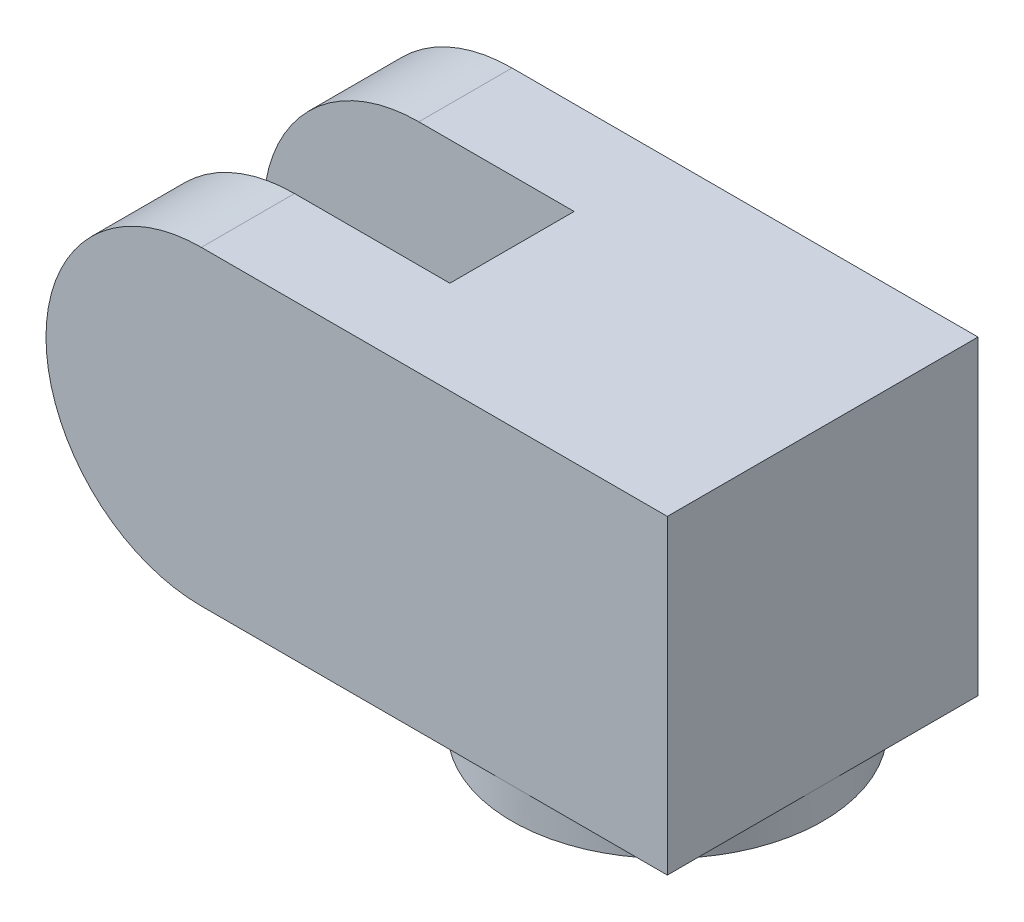
SolidWorks part; units mm, degrees
ref_plane "前视基准面" through (0, 0, 0) normal (0, 0, 1) x (1, 0, 0)
ref_plane "上视基准面" through (0, 0, 0) normal (0, 1, 0) x (1, 0, 0)
ref_plane "右视基准面" through (0, 0, 0) normal (1, 0, 0) x (0, 0, -1)
sketch "草图1" plane through (0, 0, 0) normal (0, 1, 0) x (1, 0, 0)
  line L1 (-5, 5) -> (5, 5)
  line L2 (-5, 5) -> (-5, -5)
  line L3 (-5, -5) -> (5, -5)
  line L4 (5, 5) -> (5, -5)
  dimension "D1" = 10
  dimension "D2" = 10
  dimension "D3" = 5
  dimension "D4" = 5
extrude "凸台-拉伸1" add sketch "草图1" along normal blind 10
sketch "草图2" plane through (-5, 0, 0) normal (-1, 0, 0) x (0, 0, 1)
  line L0 (-5, 0) -> (5, 0) construction
  line L1 (-5, 10) -> (-2, 10)
  line L2 (-5, 10) -> (-5, 0)
  line L3 (-5, 0) -> (-2, 0)
  line L4 (-2, 10) -> (-2, 0)
  line L6 (5, 0) -> (2, 0)
  line L7 (5, 0) -> (5, 10)
  line L8 (5, 10) -> (2, 10)
  line L9 (2, 0) -> (2, 10)
  dimension "D1" = 3
  dimension "D2" = 3
extrude "凸台-拉伸2" add sketch "草图2" along normal blind 10
sketch "草图3" plane through (0, 0, 5) normal (0, 0, 1) x (1, 0, 0)
  line L1 (-10, 10) -> (-17.0189, 10)
  line L3 (-10, 0) -> (-17.0189, 0)
  line L4 (-17.0189, 10) -> (-17.0189, 0)
  arc A0 (-10, 10) -> (-10, 0) centre (-10, 5) ccw
extrude "切除-拉伸1" cut sketch "草图3" against normal blind 10
sketch "草图4" plane through (0, 0, 0) normal (0, -1, 0) x (1, 0, 0)
  circle A0 centre (0, 0) radius 5
extrude "凸台-拉伸3" add sketch "草图4" along normal blind 1
